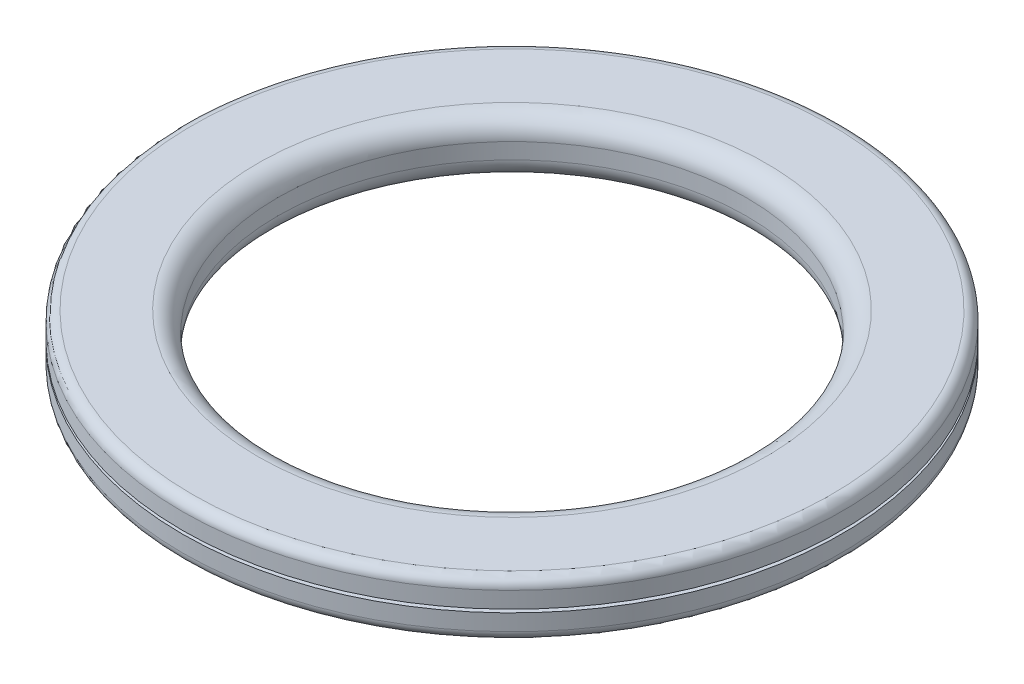
SolidWorks part; units mm, degrees
ref_plane "Front" through (0, 0, 0) normal (0, 0, 1) x (1, 0, 0)
ref_plane "Top" through (0, 0, 0) normal (0, 1, 0) x (1, 0, 0)
ref_plane "Right" through (0, 0, 0) normal (1, 0, 0) x (0, 0, -1)
sketch "Sketch1" plane through (0, 0, 0) normal (0, 1, 0) x (1, 0, 0)
  circle A0 centre (0, 0) radius 5.9
  circle A1 centre (0, 0) radius 8.3
  dimension "D1" = 11.8
  dimension "D2" = 2.4
extrude "Boss-Extrude1" add sketch "Sketch1" along normal blind 1.4
ref_plane "Plane1" through (0, 0, 8.3) normal (0, 0, 1) x (1, 0, 0)
sketch "Sketch2" plane through (0, 0, 0) normal (0, 0, 1) x (1, 0, 0)
  line L0 (8.6542, 0.74) -> (8.6542, 0.66)
  line L1 (8.3, 1.4) -> (8.3, 0) construction
  line L2 (8.6542, 0.74) -> (7.3592, 0.74)
  line L3 (7.3592, 0.74) -> (7.3592, 0.66)
  line L4 (7.3592, 0.66) -> (8.6542, 0.66)
  point P3 (8.6542, 0.7)
  point P8 (8.3, 0.7)
  dimension "D1" = 0.08
ref_axis "Axis1" through (0, 1.4, 0) along (0, -1, 0)
revolve "Cut-Revolve1" cut sketch "Sketch2" angle 360 about axis through (0, 1.4, 0) along (0, -1, 0)
sketch "Sketch3" plane through (0, 0, 0) normal (0, -1, 0) x (1, 0, 0)
  line L0 (0, 8.3) -> (0, 5.9) construction
  circle A0 centre (0, 0) radius 8.3 construction
  circle A1 centre (0, 0) radius 5.9 construction
  circle A2 centre (0, 0) radius 7.141
  circle A3 centre (0, 0) radius 7.061
  point P11 (0, 7.1)
  dimension "D1" = 0.08
extrude "Cut-Extrude1" cut sketch "Sketch3" against normal blind 0.3
fillet "Fillet1" radius 0.5 2 edges at (0, 0, 5.9) (0, 1.4, 5.9)
fillet "Fillet2" radius 0.25 2 edges at (0, 0, 8.3) (0, 1.4, 8.3)
